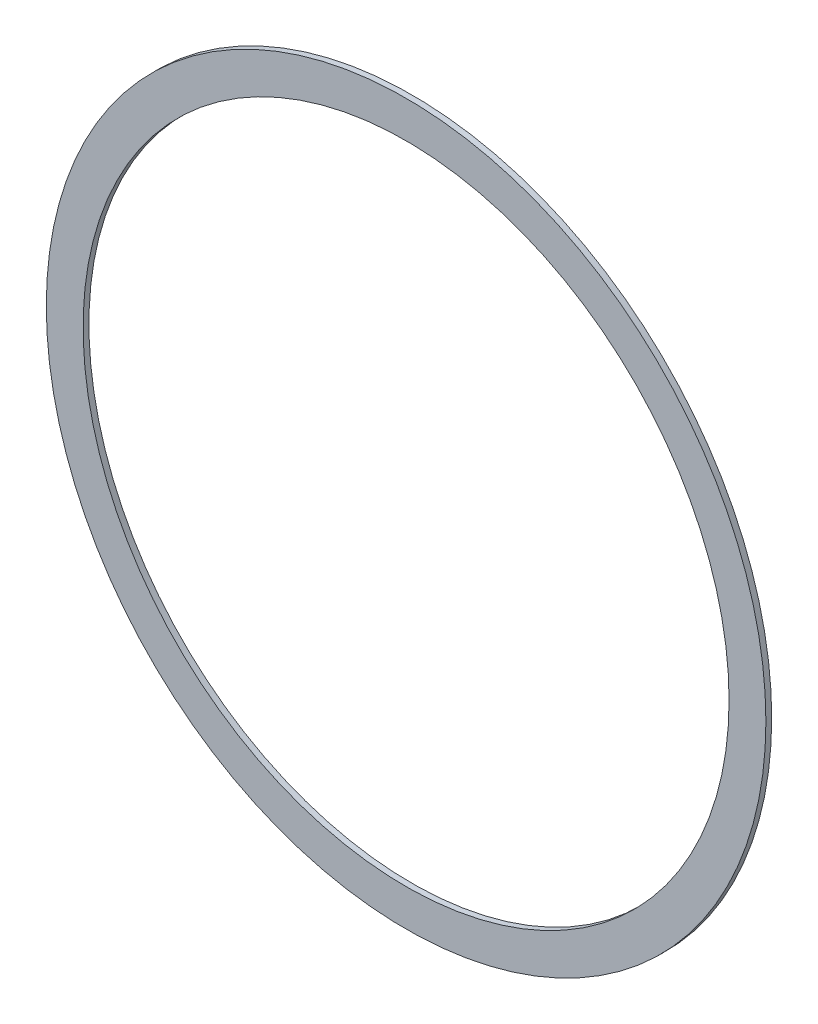
SolidWorks part; units mm, degrees
ref_plane "Front Plane" through (0, 0, 0) normal (0, 0, 1) x (1, 0, 0)
ref_plane "Top Plane" through (0, 0, 0) normal (0, 1, 0) x (1, 0, 0)
ref_plane "Right Plane" through (0, 0, 0) normal (1, 0, 0) x (0, 0, -1)
sketch "Sketch1" plane through (0, 0, 0) normal (0, 0, 1) x (1, 0, 0)
  circle A0 centre (0, 0) radius 250
  circle A1 centre (0, 0) radius 278.5
  dimension "D1" = 500
  dimension "D2" = 557
extrude "Boss-Extrude1" add sketch "Sketch1" along normal mid plane 4.5
